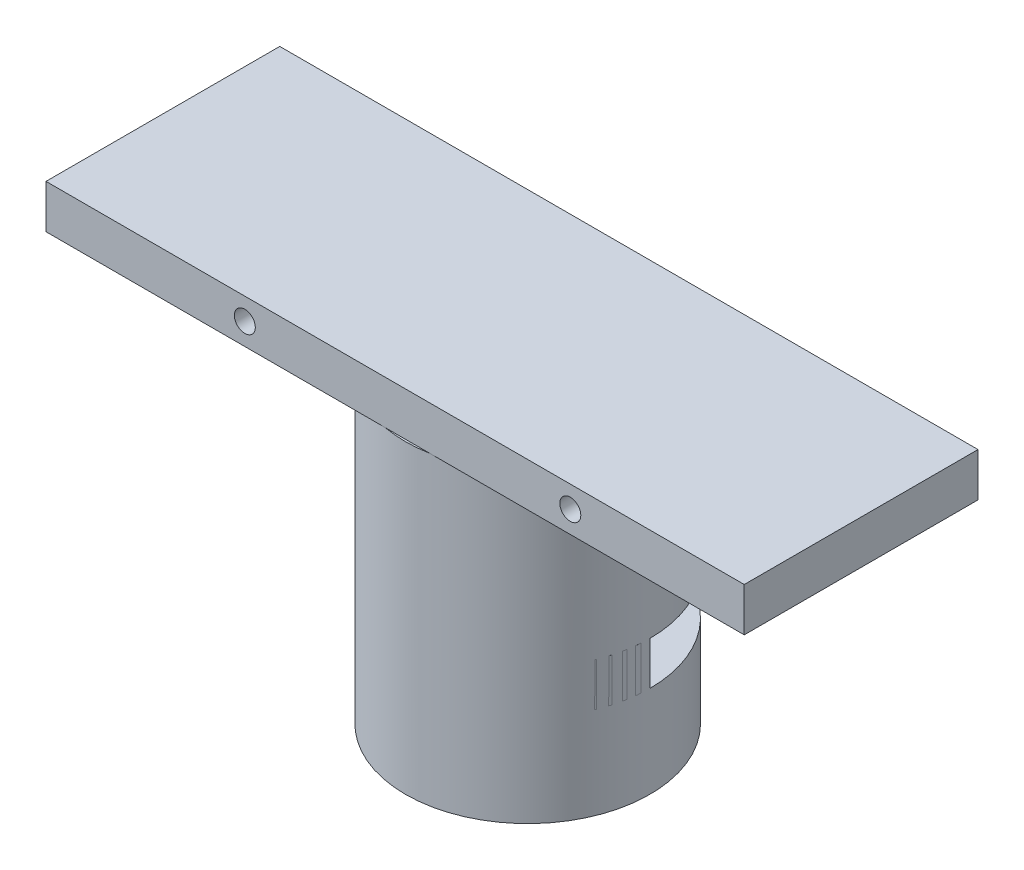
SolidWorks part; units mm, degrees
ref_plane "Front Plane" through (0, 0, 0) normal (0, 0, 1) x (1, 0, 0)
ref_plane "Top Plane" through (0, 0, 0) normal (0, 1, 0) x (1, 0, 0)
ref_plane "Right Plane" through (0, 0, 0) normal (1, 0, 0) x (0, 0, -1)
sketch "Sketch1" plane through (0, 0, 0) normal (0, 1, 0) x (1, 0, 0)
  circle A0 centre (0, 0) radius 8.89
  dimension "D1" = 17.78
extrude "Boss-Extrude2" add sketch "Sketch1" along normal blind 19.05 contours A0
sketch "Sketch3" plane through (0, 19.05, 0) normal (0, 1, 0) x (1, 0, 0)
  circle A1 centre (0, 0) radius 8.89
  dimension "D1" = 17.78
shell "Shell7" thickness 2.54
extrude "Boss-Extrude4" add sketch "Sketch3" along normal blind 3.175
sketch "Sketch4" plane through (0, 22.225, 0) normal (0, 1, 0) x (1, 0, 0)
  line L1 (24.4952, -8.7402) -> (-26.3048, -8.7402)
  line L2 (-26.3048, -8.7402) -> (-26.3048, 8.2659)
  line L3 (-26.3048, 8.2659) -> (24.4952, 8.2659)
  line L4 (24.4952, 8.2659) -> (24.4952, -8.7402)
  circle A0 centre (0, 0) radius 8.89 construction
  dimension "D2" = 8.2659
  dimension "D1" = 50.8
extrude "Boss-Extrude5" add sketch "Sketch4" along normal blind 3.175
ref_plane "Plane3" through (0, 0, -0.0186) normal (0, 0, -1) x (-1, 0, 0)
sketch "Sketch5" plane through (0, 0, -0.0186) normal (0, 0, -1) x (-1, 0, 0)
  line L0 (0, 0) -> (0, 8.255) construction
  line L1 (-8.89, 22.225) -> (-8.89, 0) construction
  line L2 (-8.89, 9.83) -> (-5.08, 9.83)
  line L3 (-8.89, 9.83) -> (-8.89, 6.68)
  line L4 (-8.89, 6.68) -> (-5.08, 6.68)
  line L5 (-5.08, 9.83) -> (-5.08, 6.68)
  line L6 (0, 8.255) -> (-8.89, 8.255) construction
  line L7 (5.08, 9.83) -> (5.08, 6.68)
  line L8 (8.89, 6.68) -> (5.08, 6.68)
  line L9 (8.89, 9.83) -> (8.89, 6.68)
  line L10 (8.89, 9.83) -> (5.08, 9.83)
  dimension "D1" = 8.255
  dimension "D2" = 3.81
  dimension "D3" = 1.575
  dimension "D4" = 3.15
revolve "Cut-Revolve1" cut sketch "Sketch5" angle 60 about L0 other way angle 60
sketch "Sketch6" plane through (0, 0, -4.4895) normal (0, 0, -1) x (-1, 0, 0)
  line L0 (-16.9199, 23.8125) -> (16.9199, 23.8125) construction
  line L1 (-16.9199, 25.4) -> (-16.9199, 22.225) construction
  line L2 (16.9199, 25.4) -> (16.9199, 22.225) construction
  line L3 (-11.8399, 25.4) -> (-11.8399, 22.225) construction
  line L4 (-16.9199, 25.4) -> (16.9199, 25.4) construction
  line L5 (-16.9199, 22.225) -> (-4.4907, 22.225) construction
  line L6 (11.8399, 25.4) -> (11.8399, 22.225) construction
  line L7 (4.4907, 22.225) -> (16.9199, 22.225) construction
  circle A0 centre (-11.8399, 23.8125) radius 0.762
  circle A1 centre (11.8399, 23.8125) radius 0.762
  dimension "D3" = 1.524
  dimension "D4" = 1.524
  dimension "D1" = 5.08
  dimension "D2" = 5.08
extrude "Cut-Extrude1" cut sketch "Sketch6" against normal through all and the other way through all contours A1 | A0
sketch "Sketch7" plane through (0, 22.225, 0) normal (0, 1, 0) x (1, 0, 0)
  line L1 (-3.2721, 8.2659) -> (3.2721, 8.2659)
  line L2 (-3.2721, 8.2659) -> (3.2721, 8.2659)
  arc A1 (3.2721, 8.2659) -> (-3.2721, 8.2659) centre (0, 0) ccw
  arc A2 (3.2721, 8.2659) -> (-3.2721, 8.2659) centre (0, 0) ccw
  dimension "D1" = 0
extrude "Cut-Extrude2" cut sketch "Sketch7" against normal through all
